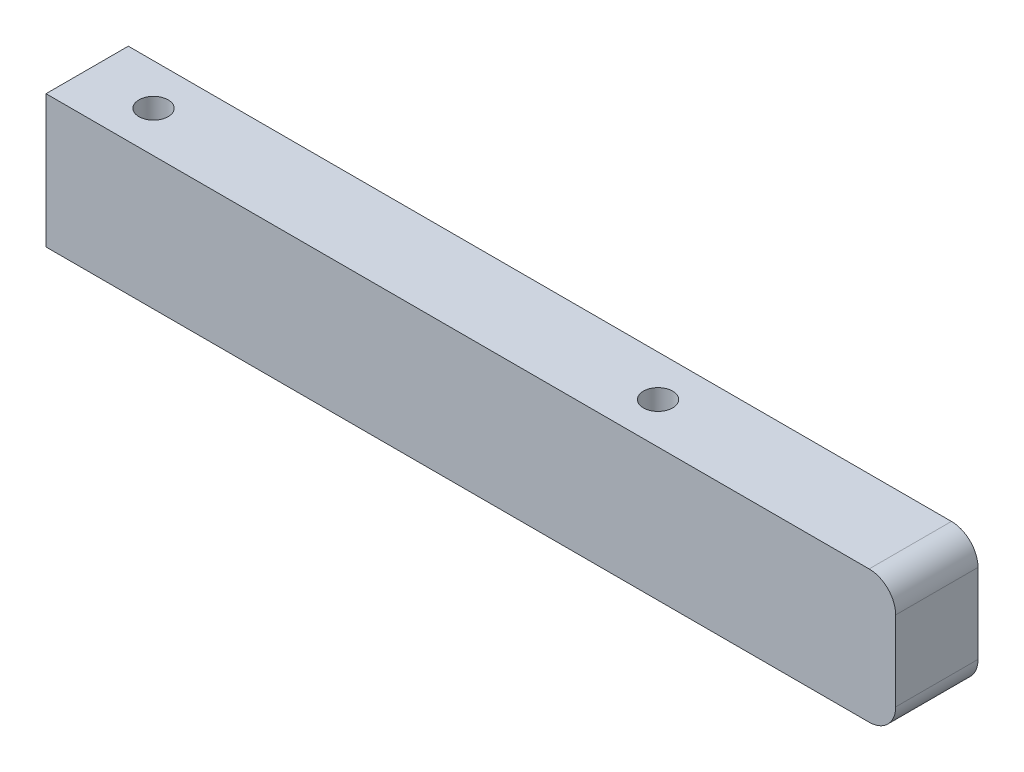
SolidWorks part; units mm, degrees
material "Cedar"
ref_plane "Front Plane" through (0, 0, 0) normal (0, 0, 1) x (1, 0, 0)
ref_plane "Top Plane" through (0, 0, 0) normal (0, 1, 0) x (1, 0, 0)
ref_plane "Right Plane" through (0, 0, 0) normal (1, 0, 0) x (0, 0, -1)
sketch "Sketch1" plane through (0, 0, 0) normal (1, 0, 0) x (0, 0, -1)
  line L1 (-7.75, -12.5) -> (7.75, -12.5)
  line L2 (-7.75, -12.5) -> (-7.75, 12.5)
  line L3 (-7.75, 12.5) -> (7.75, 12.5)
  line L4 (7.75, -12.5) -> (7.75, 12.5)
  line L5 (-7.75, -12.5) -> (7.75, 12.5) construction
  line L6 (-7.75, 12.5) -> (7.75, -12.5) construction
  point P0 (0, 0)
  dimension "D1" = 15.5
  dimension "D2" = 25
extrude "Boss-Extrude1" add sketch "Sketch1" along normal mid plane 160
sketch "Sketch6" plane through (0, -12.5, 0) normal (0, -1, 0) x (-1, 0, 0)
  line L13 (80, 7.75) -> (55, 7.75) construction
  line L14 (80, 7.75) -> (80, -7.75) construction
  line L15 (80, -7.75) -> (55, -7.75) construction
  line L16 (55, 7.75) -> (55, -7.75) construction
  line L17 (-80, -7.75) -> (80, -7.75) construction
  line L19 (-15, 7.75) -> (-40, 7.75) construction
  line L20 (-15, 7.75) -> (-15, -7.75) construction
  line L21 (-15, -7.75) -> (-40, -7.75) construction
  line L22 (-40, 7.75) -> (-40, -7.75) construction
  line L23 (-80, 7.75) -> (80, 7.75) construction
  point P0 (-27.5, 0)
  point P2 (67.5, 0)
  point P305 (67.5, 7.75)
  point P306 (55, 0)
  point P391 (-40, 0)
  point P392 (-27.5, 7.75)
  dimension "D1" = 25
  dimension "D2" = 70
hole_wizard "CBORE for M5 Hex Socket Head Cap Screw1" positions "Sketch6" profile "Sketch5" counterbore size "M5" standard "ISO" end condition through all
sketch "Sketch5" plane through (27.5, -12.5, 0) normal (1, 0, 0) x (0, 0, -1)
  line L0 (0, 0) -> (0, 25)
  line L1 (0, 25) -> (2.75, 25)
  line L3 (2.75, 25) -> (2.75, 5.4)
  line L4 (2.75, 5.4) -> (5, 5.4)
  line L5 (5, 5.4) -> (5, 0)
  line L7 (5, 0) -> (0, 0)
  line L11 (0, -6.35) -> (0, 107.95) construction
  dimension "Thru Hole Dia." = 5.5
  dimension "Thru Hole Depth" = 25
  dimension "C'Bore Dia." = 10
  dimension "C'Bore Depth" = 5.4
fillet "Fillet1" radius 5 1 edges at (80, -12.5, 0)
fillet "Fillet2" radius 5 1 edges at (80, 12.5, 0)
